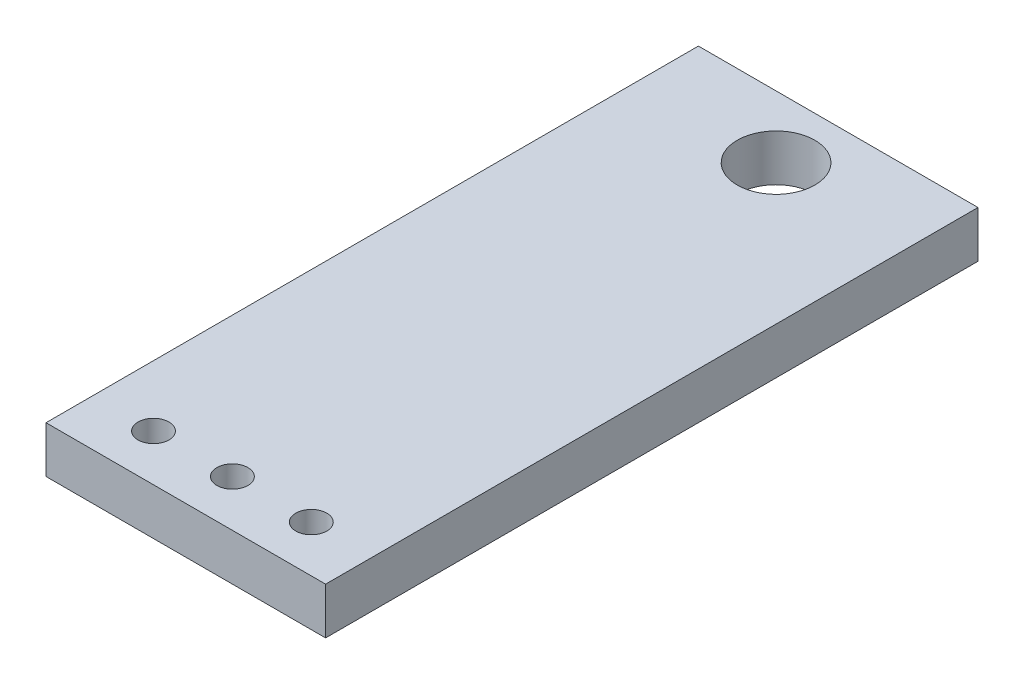
SolidWorks part; units mm, degrees
ref_plane "Alzado" through (0, 0, 0) normal (0, 0, 1) x (1, 0, 0)
ref_plane "Planta" through (0, 0, 0) normal (0, 1, 0) x (1, 0, 0)
ref_plane "Vista lateral" through (0, 0, 0) normal (1, 0, 0) x (0, 0, -1)
sketch "Croquis1" plane through (0, 0, 0) normal (0, 1, 0) x (1, 0, 0)
  line L0 (-7.5811, 8.5) -> (6.973, 8.5) construction
  line L1 (-4.5, -10.5) -> (4.5, -10.5)
  line L2 (-4.5, -10.5) -> (-4.5, 10.5)
  line L3 (-4.5, 10.5) -> (4.5, 10.5)
  line L4 (4.5, -10.5) -> (4.5, 10.5)
  line L5 (-4.5, -10.5) -> (4.5, 10.5) construction
  line L6 (-4.5, 10.5) -> (4.5, -10.5) construction
  line L7 (0, 13.0338) -> (0, -14.5743) construction
  line L8 (-6.1578, -9) -> (6.5395, -9) construction
  circle A0 centre (0, 8.5) radius 1.25
  circle A1 centre (-2.54, -9) radius 0.5
  circle A2 centre (0, -9) radius 0.5
  circle A3 centre (2.54, -9) radius 0.5
  point P0 (0, 0)
  point P10 (0, 8.5)
  point P17 (0, -9)
  dimension "D4" = 2.5
  dimension "D6" = 1
  dimension "D7" = 1
  dimension "D8" = 1
  dimension "D1" = 9
  dimension "D2" = 21
  dimension "D3" = 2
  dimension "D5" = 1.5
  dimension "D9" = 2.54
  dimension "D10" = 2.54
extrude "Saliente-Extruir1" add sketch "Croquis1" along normal blind 1.5
